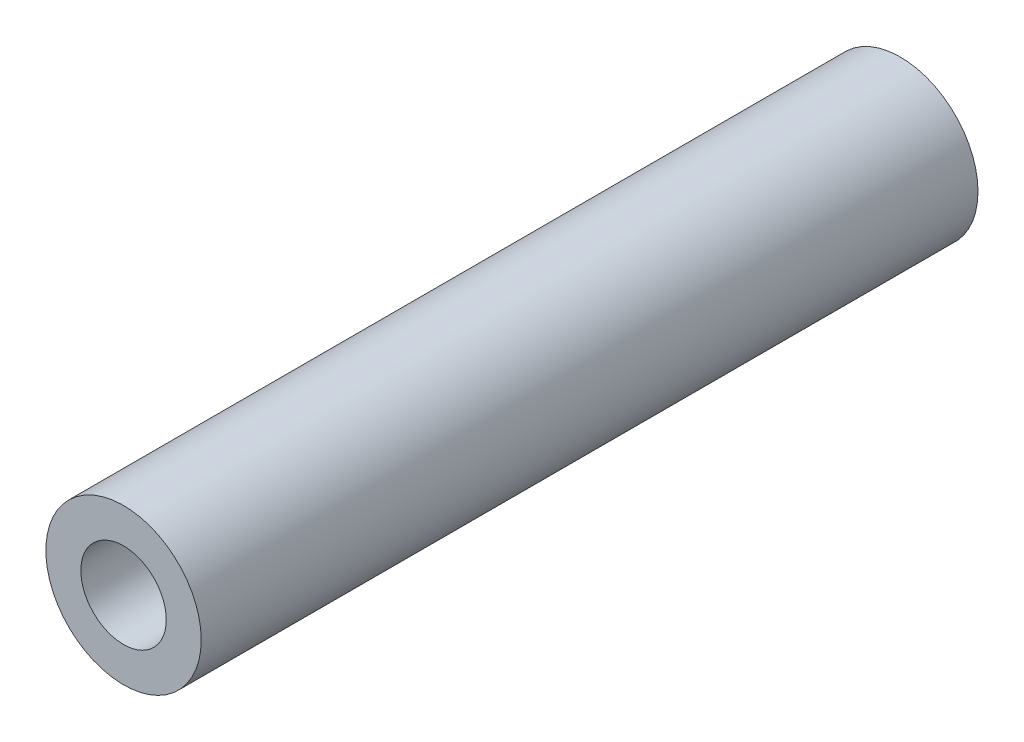
SolidWorks part; units mm, degrees
ref_plane "正面" through (0, 0, 0) normal (0, 0, 1) x (1, 0, 0)
ref_plane "平面" through (0, 0, 0) normal (0, 1, 0) x (1, 0, 0)
ref_plane "右側面" through (0, 0, 0) normal (1, 0, 0) x (0, 0, -1)
sketch "ｽｹｯﾁ1" plane through (0, 0, 0) normal (0, 0, 1) x (1, 0, 0)
  circle A0 centre (0, 0) radius 3
  dimension "D1" = 6
extrude "ﾎﾞｽ - 押し出し1" add sketch "ｽｹｯﾁ1" along normal mid plane 30
sketch "ｽｹｯﾁ2" plane through (0, 0, 15) normal (0, 0, 1) x (1, 0, 0)
  circle A0 centre (0, 0) radius 3
  dimension "D1" = 6
hole_wizard "M4x0.7 ねじ穴1" positions "3Dｽｹｯﾁ1" profile "ｽｹｯﾁ6" tap size "M4x0.7" standard "JIS"
sketch3d "3Dｽｹｯﾁ1"
  line L0 (0, 0, 15) -> (0, 0, -15) construction
  point P0 (0, 0, 15)
  point P3 (0, 0, -15)
  point P7 (8.5233, 2.0884, 0)
sketch "ｽｹｯﾁ6" plane through (0, 0, 15) normal (1, 0, 0) x (0, -1, 0)
  line L0 (0, 0) -> (0, 9.4914)
  line L1 (0, 9.4914) -> (1.65, 8.5)
  line L2 (1.65, 8.5) -> (1.65, 0)
  line L5 (1.65, 0) -> (0, 0)
  line L10 (0, 9.4914) -> (-1.65, 8.5) construction
  line L11 (0, -6.35) -> (0, 107.95) construction
  dimension "ねじ下穴ﾄﾞﾘﾙ直径" = 3.3
  dimension "ねじ下穴ﾄﾞﾘﾙの深さ" = 8.5
  dimension "ﾄﾞﾘﾙ角度" = 118
cosmetic thread "穴のねじ山1"
cosmetic thread "穴のねじ山2"
cosmetic thread "穴のねじ山3"
sketch "ｽｹｯﾁ3" plane through (0, 0, 30) normal (0, 0, 1) x (1, 0, 0)
  circle A0 centre (0, 0) radius 2.45
  dimension "D1" = 4.9
sketch "ｽｹｯﾁ4" plane through (0, 0, -15) normal (0, 0, -1) x (-1, 0, 0)
  circle A0 centre (0, 0) radius 2.45
sketch "ｽｹｯﾁ5" plane through (0, 0, 36) normal (0, 0, 1) x (1, 0, 0)
  circle A0 centre (0, 0) radius 2.45
